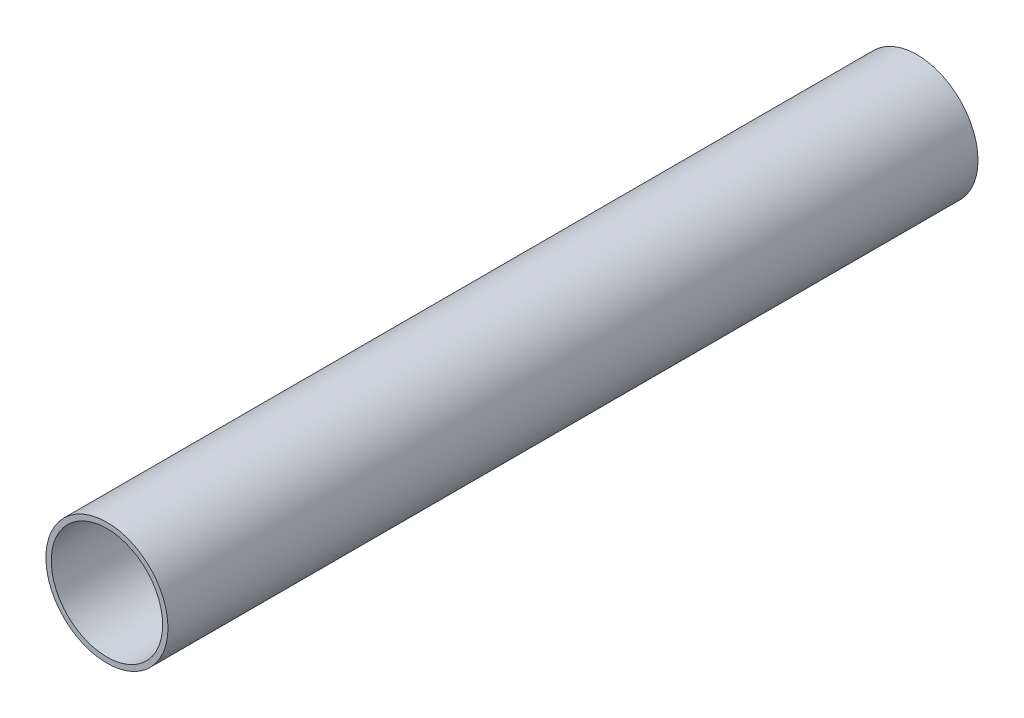
SolidWorks part; units mm, degrees
ref_plane "Front Plane" through (0, 0, 0) normal (0, 0, 1) x (1, 0, 0)
ref_plane "Top Plane" through (0, 0, 0) normal (0, 1, 0) x (1, 0, 0)
ref_plane "Right Plane" through (0, 0, 0) normal (1, 0, 0) x (0, 0, -1)
sketch "Sketch1" plane through (0, 0, 0) normal (0, 0, 1) x (1, 0, 0)
  circle A0 centre (0, 0) radius 30.15
  circle A1 centre (0, 0) radius 27.5
extrude "Boss-Extrude1" add sketch "Sketch1" along normal blind 400
